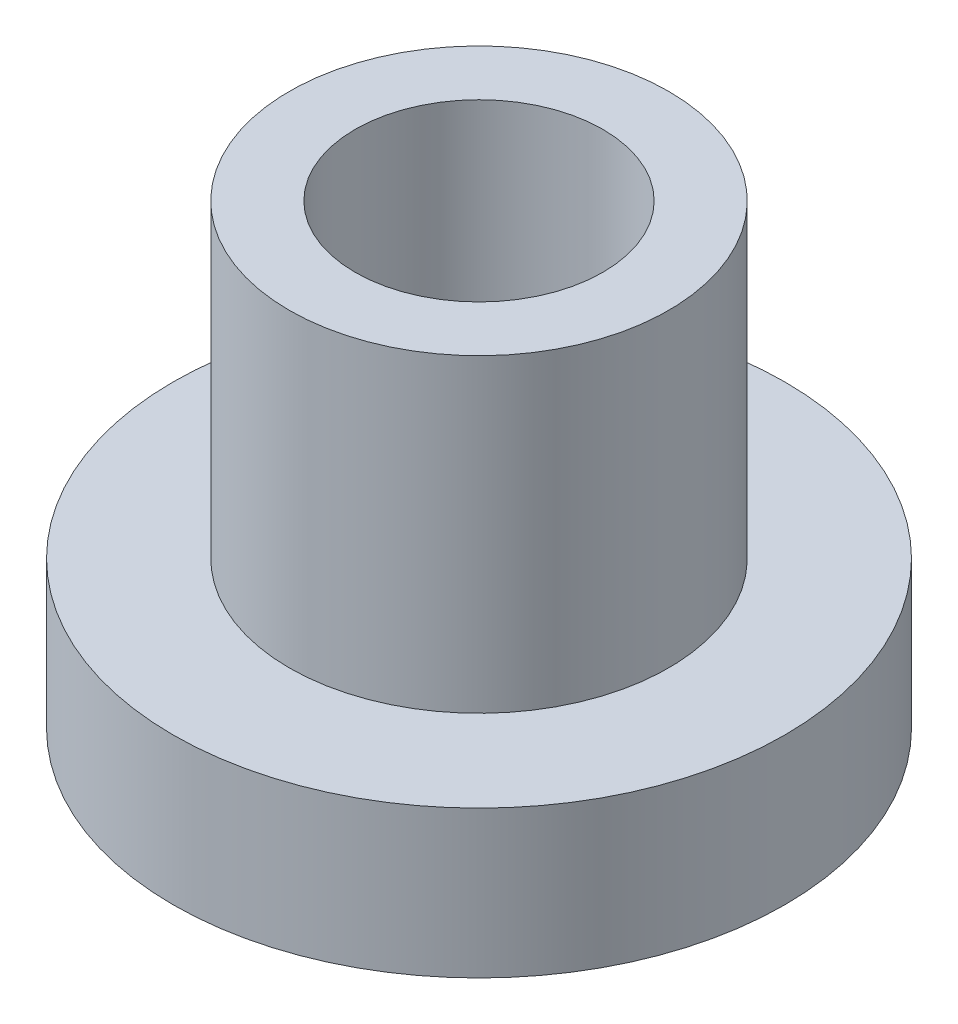
SolidWorks part; units mm, degrees
material "Brass"
ref_plane "Front Plane" through (0, 0, 0) normal (0, 0, 1) x (1, 0, 0)
ref_plane "Top Plane" through (0, 0, 0) normal (0, 1, 0) x (1, 0, 0)
ref_plane "Right Plane" through (0, 0, 0) normal (1, 0, 0) x (0, 0, -1)
sketch "Sketch1" plane through (0, 0, 0) normal (0, 1, 0) x (1, 0, 0)
  circle A0 centre (0, 0) radius 3.95
  circle A1 centre (0, 0) radius 1.6
  dimension "D1" = 7.9
  dimension "D2" = 3.2
extrude "Boss-Extrude1" add sketch "Sketch1" along normal blind 1.9
sketch "Sketch2" plane through (0, 1.9, 0) normal (0, 1, 0) x (1, 0, 0)
  circle A0 centre (0, 0) radius 2.45
  circle A1 centre (0, 0) radius 1.6 construction
  circle A2 centre (0, 0) radius 1.6
  dimension "D1" = 4.9
extrude "Boss-Extrude2" add sketch "Sketch2" along normal blind 4
